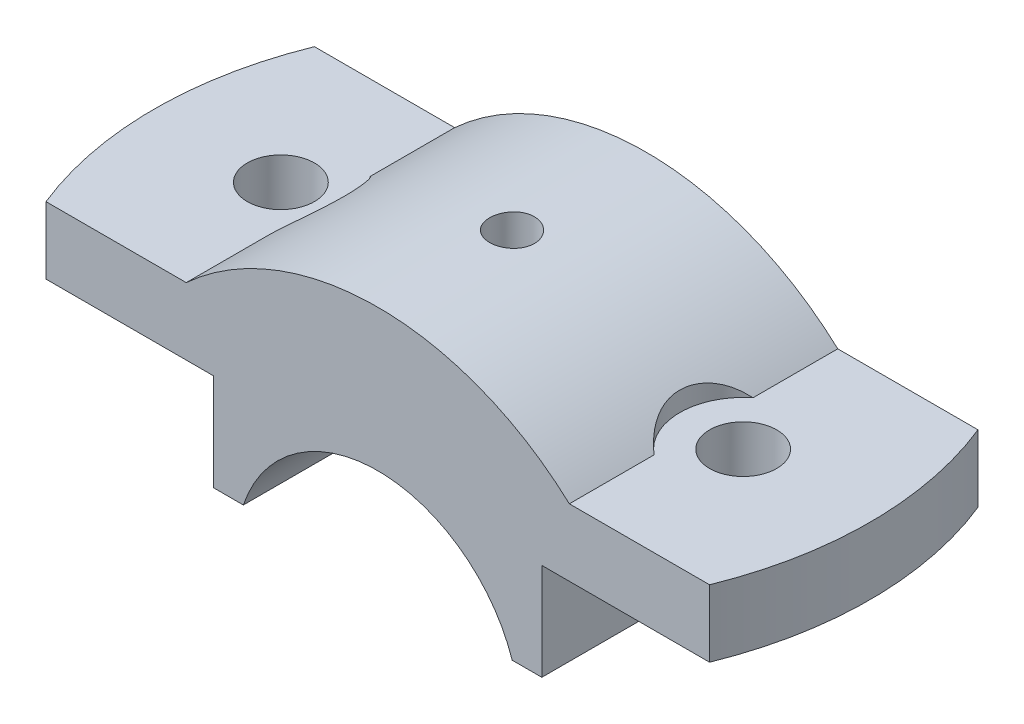
SolidWorks part; units mm, degrees
ref_plane "Front Plane" through (0, 0, 0) normal (0, 0, 1) x (1, 0, 0)
ref_plane "Top Plane" through (0, 0, 0) normal (0, 1, 0) x (1, 0, 0)
ref_plane "Right Plane" through (0, 0, 0) normal (1, 0, 0) x (0, 0, -1)
sketch "Sketch1" plane through (0, 0, 0) normal (0, 0, 1) x (1, 0, 0)
  line L0 (-22, 6) -> (-18.0278, 6)
  line L1 (-22, 6) -> (-22, 19)
  line L2 (-22, 19) -> (-50, 19)
  line L3 (-50, 19) -> (-50, 28)
  line L4 (-50, 28) -> (-25.6905, 28)
  line L5 (0, 86.9237) -> (0, -96.9131) construction
  line L6 (99.4761, 0) -> (-113.4002, 0) construction
  line L7 (22, 6) -> (18.0278, 6)
  line L8 (22, 6) -> (22, 19)
  line L9 (50, 19) -> (50, 28)
  line L10 (22, 19) -> (50, 19)
  line L11 (50, 28) -> (25.6905, 28)
  arc A0 (18.0278, 6) -> (-18.0278, 6) centre (0, 0) ccw
  arc A1 (25.6905, 28) -> (-25.6905, 28) centre (0, 0) ccw
  dimension "D1" = 6
  dimension "D4" = 19
  dimension "D5" = 38
  dimension "D2" = 13
  dimension "D3" = 9
  dimension "D6" = 44
  dimension "D7" = 50
extrude "Boss-Extrude1" add sketch "Sketch1" along normal mid plane 36
sketch "Sketch2" plane through (0, 28, 0) normal (0, 1, 0) x (1, 0, 0)
  circle A0 centre (-31, 0) radius 4.5
  circle A1 centre (31, 0) radius 4.5
  dimension "D1" = 9
  dimension "D4" = 9
  dimension "D2" = 31
  dimension "D3" = 62
extrude "Cut-Extrude1" cut sketch "Sketch2" against normal through all
sketch "Sketch4" plane through (0, 28, 0) normal (0, 1, 0) x (1, 0, 0)
  circle A0 centre (-31, 0) radius 8.5
extrude "Cut-Extrude2" cut sketch "Sketch4" along normal through all
sketch "Sketch5" plane through (0, 28, 0) normal (0, 1, 0) x (1, 0, 0)
  line L0 (-25.6905, 18) -> (-50, 18) construction
  line L1 (-50, -18) -> (-50, 18) construction
  line L2 (-25.6905, -18) -> (-50, -18) construction
  line L3 (50, 18) -> (25.6905, 18) construction
  line L4 (50, -18) -> (50, 18) construction
  line L5 (50, -18) -> (25.6905, -18) construction
  line L6 (-44.4972, 18) -> (-50, 18)
  line L7 (-50, -18) -> (-50, 18)
  line L8 (-44.4972, -18) -> (-50, -18)
  line L9 (50, 18) -> (44.4972, 18)
  line L10 (50, -18) -> (50, 18)
  line L11 (50, -18) -> (44.4972, -18)
  arc A0 (-44.4972, 18) -> (-44.4972, -18) centre (0, 0) ccw
  arc A1 (44.4972, -18) -> (44.4972, 18) centre (0, 0) ccw
extrude "Cut-Extrude3" cut sketch "Sketch5" against normal through all
sketch "Sketch6" plane through (0, 28, 0) normal (0, 1, 0) x (1, 0, 0)
  circle A0 centre (31, 0) radius 8.5
extrude "Cut-Extrude4" cut sketch "Sketch6" along normal through all
hole_wizard "CBORE for M5 Hex Head Bolt1" positions "3DSketch1" profile "Sketch8" counterbore size "M5" standard "ANSI Metric" end condition through all
sketch3d "3DSketch1"
  point P0 (0, 38, 0)
  dimension "D1" = 0
  dimension "D2" = 0
sketch "Sketch8" plane through (0, 38, 0) normal (1, 0, 0) x (0, 0, 1)
  line L0 (0, 0) -> (0, 32)
  line L1 (0, 32) -> (2.5, 32)
  line L2 (2.5, 13.495) -> (2.5, 32)
  line L3 (2.5, 13.495) -> (2.995, 13)
  line L4 (2.995, 13) -> (3, 13)
  line L5 (3, 13) -> (3, 0)
  line L7 (0, 0) -> (3, 0)
  line L9 (-2.5, 13.495) -> (-2.995, 13) construction
  line L11 (0, -6.35) -> (0, 107.95) construction
  dimension "Thru Hole Dia." = 5
  dimension "Thru Hole Depth" = 32
  dimension "C'Bore Dia." = 6
  dimension "C'Bore Depth" = 13
  dimension "Mid C'Sink Dia." = 5.99
  dimension "Mid C'Sink Angle" = 90
